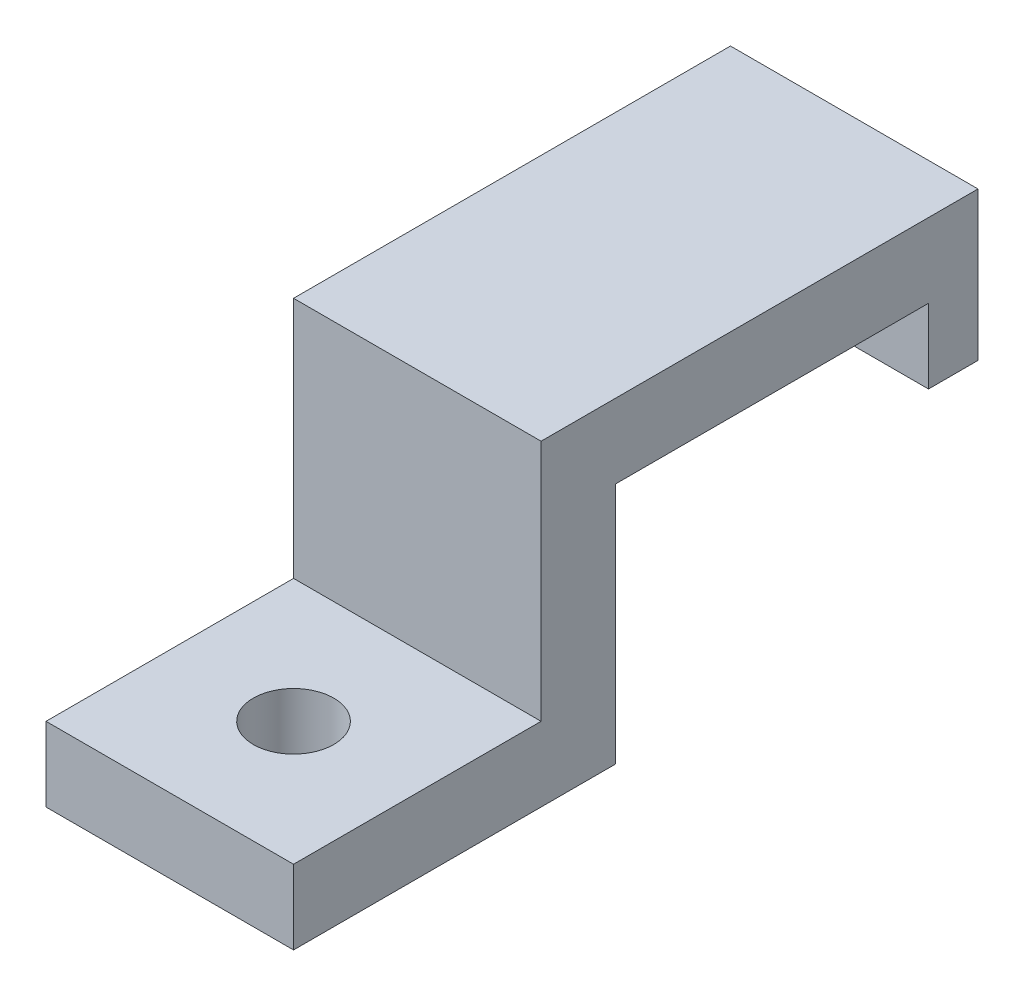
SolidWorks part; units mm, degrees
ref_plane "Alzado" through (0, 0, 0) normal (0, 0, 1) x (1, 0, 0)
ref_plane "Planta" through (0, 0, 0) normal (0, 1, 0) x (1, 0, 0)
ref_plane "Vista lateral" through (0, 0, 0) normal (1, 0, 0) x (0, 0, -1)
sketch "Croquis2" plane through (0, 0, 0) normal (1, 0, 0) x (0, 0, -1)
  line L0 (0, 0) -> (13, 0)
  line L1 (13, 0) -> (13, 9.8)
  line L2 (13, 9.8) -> (25.65, 9.8)
  line L3 (25.65, 9.8) -> (25.65, 12.8)
  line L4 (25.65, 12.8) -> (10, 12.8)
  line L5 (10, 12.8) -> (10, 3)
  line L6 (10, 3) -> (0, 3)
  line L7 (0, 3) -> (0, 0)
  dimension "D1" = 12.65
  dimension "D2" = 3
  dimension "D3" = 3
  dimension "D4" = 3
  dimension "D5" = 10
  dimension "D6" = 9.8
extrude "Saliente-Extruir1" add sketch "Croquis2" along normal blind 10
sketch "Croquis4" plane through (0, 0, 0) normal (1, 0, 0) x (0, 0, -1)
  line L0 (13, 9.8) -> (25.65, 9.8) construction
  line L1 (25.65, 12.8) -> (27.65, 12.8)
  line L2 (25.65, 12.8) -> (25.65, 6.8)
  line L3 (25.65, 6.8) -> (27.65, 6.8)
  line L4 (27.65, 12.8) -> (27.65, 6.8)
  dimension "D1" = 2
  dimension "D2" = 3
extrude "Saliente-Extruir2" add sketch "Croquis4" along normal through all
sketch "Croquis5" plane through (0, 3, 0) normal (0, 1, 0) x (1, 0, 0)
  line L0 (0, 0) -> (10, 10) construction
  circle A0 centre (5, 5) radius 1.625
  dimension "D1" = 3.25
extrude "Cortar-Extruir1" cut sketch "Croquis5" against normal through all
